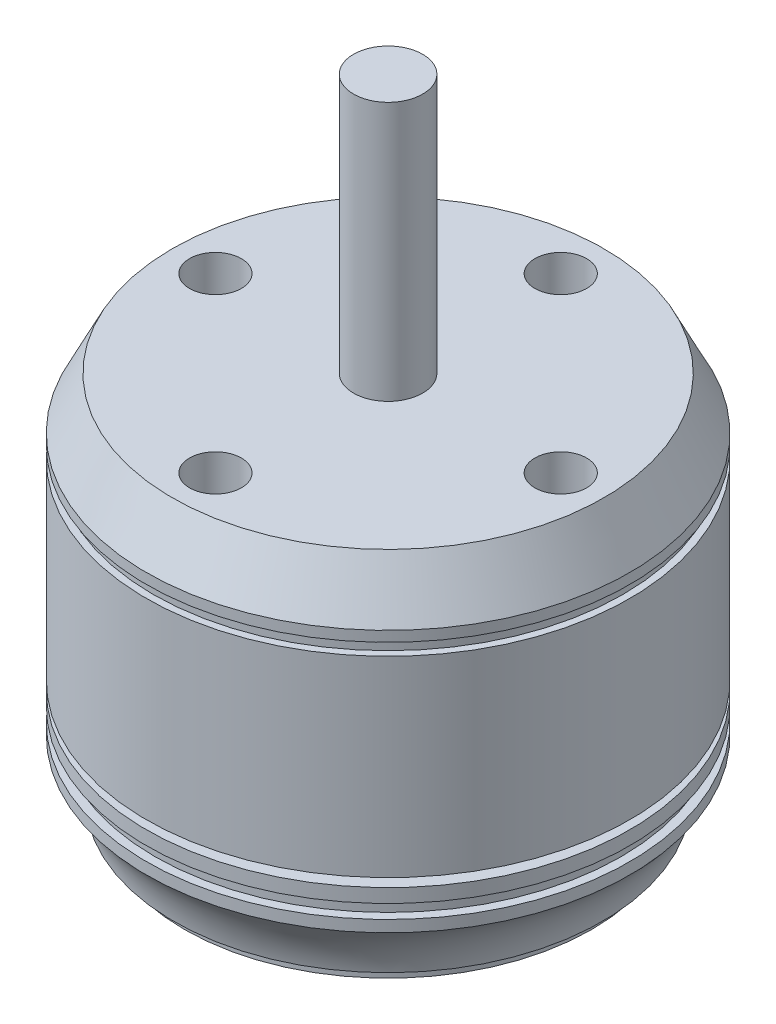
SolidWorks part; units mm, degrees
ref_plane "Front Plane" through (0, 0, 0) normal (0, 0, 1) x (1, 0, 0)
ref_plane "Top Plane" through (0, 0, 0) normal (0, 1, 0) x (1, 0, 0)
ref_plane "Right Plane" through (0, 0, 0) normal (1, 0, 0) x (0, 0, -1)
sketch "Sketch1" plane through (0, 0, 0) normal (0, 0, 1) x (1, 0, 0)
  line L0 (0, 0) -> (11.8, 0)
  line L1 (11.8, 0) -> (11.8, 0.7)
  line L2 (11.8, 0.7) -> (12.4, 0.7)
  line L5 (14, 6.1) -> (2, 6.1)
  line L6 (2, 6.1) -> (2, 6.6)
  line L7 (2, 6.6) -> (14, 6.6)
  line L8 (14, 6.6) -> (14, 17.7)
  line L9 (14, 17.7) -> (13.6, 17.7)
  line L10 (13.6, 17.7) -> (13.6, 18.4)
  line L11 (13.6, 18.4) -> (14, 18.4)
  line L12 (14, 18.4) -> (14, 19)
  line L13 (14, 19) -> (12.5, 22)
  line L14 (12.5, 22) -> (2, 22)
  line L15 (2, 22) -> (2, 37)
  line L16 (2, 37) -> (0, 37)
  line L17 (0, 37) -> (0, 0)
  line L18 (14, 3.83) -> (14, 4.5)
  line L19 (14, 4.5) -> (13.5, 4.5)
  line L20 (13.5, 4.5) -> (13.5, 5.3)
  line L21 (13.5, 5.3) -> (14, 5.3)
  line L22 (14, 5.3) -> (14, 6.1)
  arc A0 (14, 3.83) -> (12.4, 0.7) centre (18.3081, -0.3462) ccw
  dimension "D6" = 6
  dimension "D1" = 11.8
  dimension "D2" = 12.4
  dimension "D3" = 0.7
  dimension "D4" = 14
  dimension "D5" = 3.83
  dimension "D7" = 4.5
  dimension "D8" = 0.8
  dimension "D9" = 13.5
  dimension "D10" = 13.6
  dimension "D11" = 2
  dimension "D12" = 6.1
  dimension "D13" = 0.5
  dimension "D14" = 17.7
  dimension "D15" = 18.4
  dimension "D16" = 19
  dimension "D17" = 22
  dimension "D18" = 12.5
  dimension "D19" = 37
revolve "Revolve1" add sketch "Sketch1" angle 360 about L17
sketch "Sketch2" plane through (0, 0, 0) normal (0, -1, 0) x (1, 0, 0)
  line L0 (-9.5, 0) -> (9.5, 0) construction
  line L1 (0, 8) -> (0, -8) construction
  circle A0 centre (0, 8) radius 1.5
  circle A1 centre (9.5, 0) radius 1.5
  circle A2 centre (0, -8) radius 1.5
  circle A3 centre (-9.5, 0) radius 1.5
  point P5 (0, 0)
  point P8 (0, 0)
  dimension "D3" = 3
  dimension "D1" = 19
  dimension "D2" = 16
extrude "Cut-Extrude1" cut sketch "Sketch2" against normal blind 3
sketch "Sketch3" plane through (0, 22, 0) normal (0, 1, 0) x (1, 0, 0)
  circle A0 centre (0, 0) radius 10 construction
  circle A1 centre (0, 10) radius 1.5
  circle A2 centre (10, 0) radius 1.5
  circle A3 centre (0, -10) radius 1.5
  circle A4 centre (-10, 0) radius 1.5
  dimension "D1" = 20
  dimension "D2" = 3
extrude "Cut-Extrude2" cut sketch "Sketch3" against normal blind 2.8
